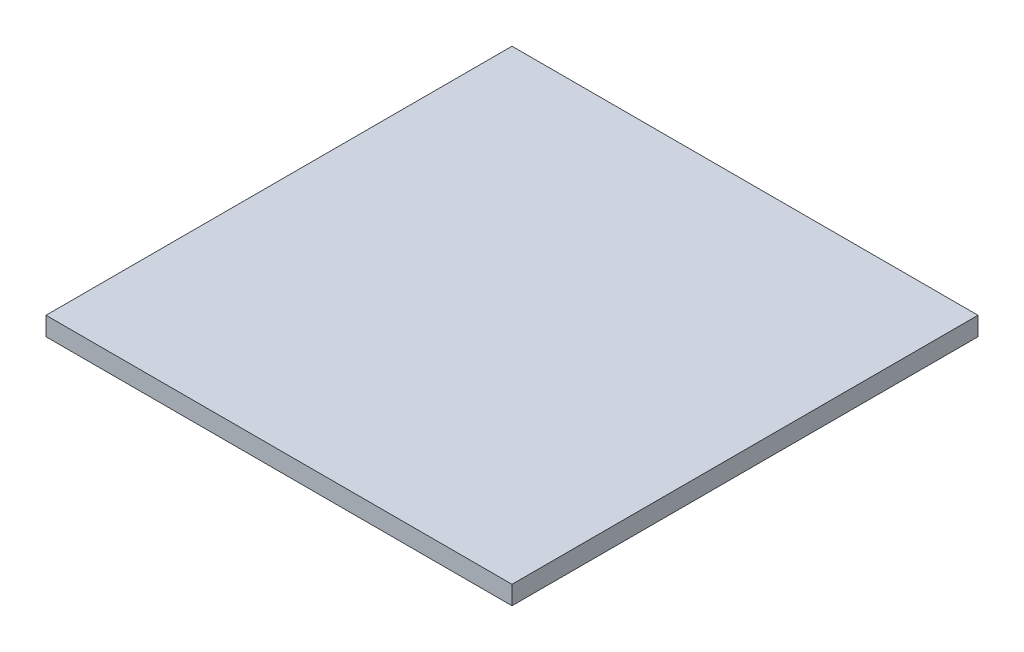
SolidWorks part; units mm, degrees
material "Silicon"
ref_plane "Plan de face" through (0, 0, 0) normal (0, 0, 1) x (1, 0, 0)
ref_plane "Plan de dessus" through (0, 0, 0) normal (0, 1, 0) x (1, 0, 0)
ref_plane "Plan de droite" through (0, 0, 0) normal (1, 0, 0) x (0, 0, -1)
sketch "Sketch1" plane through (0, 0, 0) normal (0, 1, 0) x (1, 0, 0)
  line L1 (-2.5, 2.5) -> (2.5, 2.5)
  line L2 (-2.5, 2.5) -> (-2.5, -2.5)
  line L3 (-2.5, -2.5) -> (2.5, -2.5)
  line L4 (2.5, 2.5) -> (2.5, -2.5)
  point P4 (0, 2.5)
  point P10 (-2.5, 0)
  dimension "D1" = 5
  dimension "D2" = 5
extrude "Boss-Extrude1" add sketch "Sketch1" along normal blind 0.2
